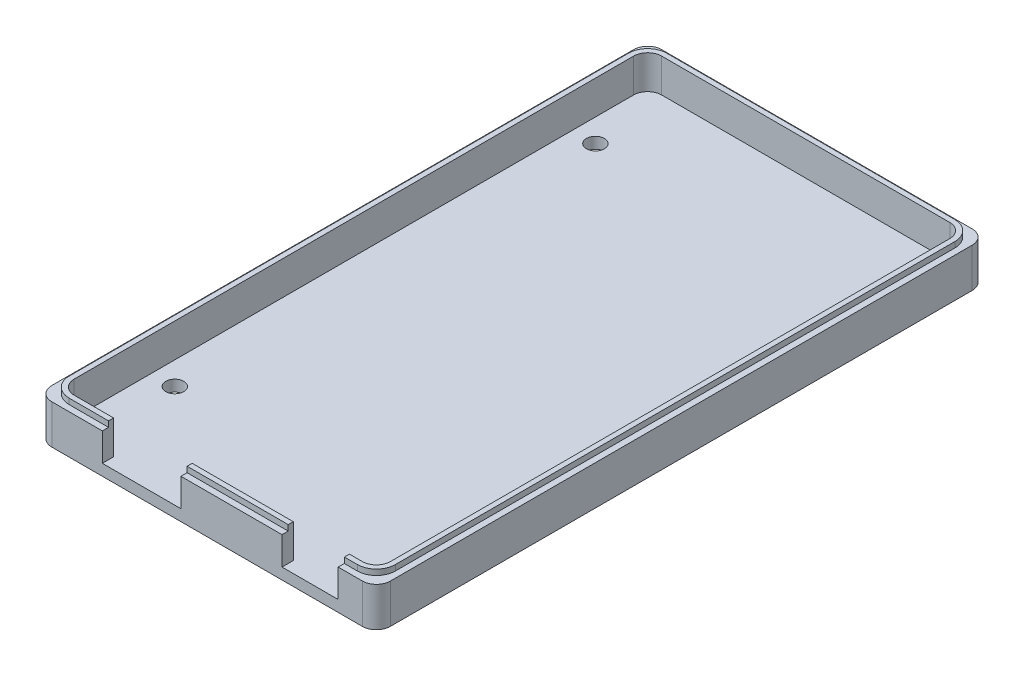
SolidWorks part; units mm, degrees
ref_plane "Front Plane" through (0, 0, 0) normal (0, 0, 1) x (1, 0, 0)
ref_plane "Top Plane" through (0, 0, 0) normal (0, 1, 0) x (1, 0, 0)
ref_plane "Right Plane" through (0, 0, 0) normal (1, 0, 0) x (0, 0, -1)
sketch "Sketch1" plane through (0, 0, 0) normal (0, 1, 0) x (1, 0, 0)
  line L0 (-12.8, 0) -> (-32.3, 0)
  line L1 (0, 0) -> (-3.8, 0)
  line L2 (0, 0) -> (0, 101.6)
  line L3 (0, 101.6) -> (-53.3, 101.6)
  line L4 (-53.3, 0) -> (-53.3, 101.6)
  line L5 (0, 0) -> (-53.3, 101.6) construction
  line L6 (0, 101.6) -> (-53.3, 0) construction
  line L7 (-44.3, -7) -> (-32.3, -7)
  line L8 (-44.3, -7) -> (-44.3, 0)
  line L10 (-32.3, -7) -> (-32.3, 0)
  line L11 (-44.3, -7) -> (-32.3, 0) construction
  line L12 (-44.3, 0) -> (-32.3, -7) construction
  line L13 (-3.8, -1.5) -> (-12.8, -1.5)
  line L14 (-3.8, -1.5) -> (-3.8, 0)
  line L16 (-12.8, -1.5) -> (-12.8, 0)
  line L17 (-3.8, -1.5) -> (-12.8, 0) construction
  line L18 (-3.8, 0) -> (-12.8, -1.5) construction
  line L19 (-44.3, 0) -> (-53.3, 0)
  circle A0 centre (-50.7, 14.8) radius 1.6
  circle A1 centre (-50.7, 89.7) radius 1.6
  circle A2 centre (-2.5, 13.5) radius 1.6
  circle A3 centre (-2.5, 96.52) radius 1.6
  circle A4 centre (-35.5, 65.6) radius 1.6
  circle A5 centre (-7.6, 65.6) radius 1.6
  point P4 (-26.65, 50.8)
  point P22 (-8.3, -0.75)
  point P23 (0, 0)
  point P24 (0, 0)
  point P30 (-38.3, -3.5)
  dimension "D11" = 3.2
  dimension "D1" = 53.3
  dimension "D2" = 101.6
  dimension "D3" = 2.5
  dimension "D4" = 5.1
  dimension "D5" = 27.9
  dimension "D6" = 15.2
  dimension "D7" = 13.5
  dimension "D8" = 1.3
  dimension "D9" = 50.8
  dimension "D10" = 24.1
  dimension "D12" = 9
  dimension "D13" = 12
  dimension "D14" = 3.8
  dimension "D15" = 9
  dimension "D16" = 7
  dimension "D17" = 1.5
  dimension "D18" = 96.52
sketch "Sketch2" plane through (0, 0, 0) normal (0, 1, 0) x (1, 0, 0)
  line L0 (0, 101.6) -> (-53.3, 101.6) construction
  line L1 (-53.3, 0) -> (-53.3, 101.6) construction
  line L2 (-44.3, 0) -> (-53.3, 0) construction
  line L3 (-44.3, -7) -> (-44.3, 0) construction
  line L4 (-12.8, -1.5) -> (-12.8, 0) construction
  line L5 (0, 0) -> (-3.8, 0) construction
  line L6 (-3.8, -1.5) -> (-3.8, 0) construction
  line L7 (-3.8, -1.5) -> (-12.8, -1.5) construction
  line L8 (0, 0) -> (0, 101.6) construction
  line L9 (-44.3, -7) -> (-32.3, -7) construction
  line L10 (-32.3, -7) -> (-32.3, 0) construction
  line L11 (-12.8, 0) -> (-32.3, 0) construction
  line L12 (0, 101.6) -> (-53.3, 101.6)
  line L13 (-53.3, 0) -> (-53.3, 101.6)
  line L14 (-44.3, 0) -> (-53.3, 0)
  line L15 (-44.3, -7) -> (-44.3, 0)
  line L16 (-12.8, -1.5) -> (-12.8, 0)
  line L17 (0, 0) -> (-3.8, 0)
  line L18 (-3.8, -1.5) -> (-3.8, 0)
  line L19 (-3.8, -1.5) -> (-12.8, -1.5)
  line L20 (0, 0) -> (0, 101.6)
  line L21 (-44.3, -7) -> (-32.3, -7)
  line L22 (-32.3, -7) -> (-32.3, 0)
  line L23 (-12.8, 0) -> (-32.3, 0)
  line L24 (-53.3, 67.5) -> (0, 67.5)
  line L25 (-4, 15) -> (-24, 15)
  line L26 (-4, 15) -> (-4, 30)
  line L27 (-4, 30) -> (-24, 30)
  line L28 (-24, 15) -> (-24, 30)
  line L29 (-4, 15) -> (-24, 30) construction
  line L30 (-4, 30) -> (-24, 15) construction
  line L31 (-29.3, 15) -> (-49.3, 15)
  line L32 (-29.3, 15) -> (-29.3, 30)
  line L33 (-29.3, 30) -> (-49.3, 30)
  line L34 (-49.3, 15) -> (-49.3, 30)
  line L35 (-29.3, 15) -> (-49.3, 30) construction
  line L36 (-29.3, 30) -> (-49.3, 15) construction
  line L37 (-4, 35) -> (-24, 35)
  line L38 (-4, 35) -> (-4, 50)
  line L39 (-4, 50) -> (-24, 50)
  line L40 (-24, 35) -> (-24, 50)
  line L41 (-4, 35) -> (-24, 50) construction
  line L42 (-4, 50) -> (-24, 35) construction
  line L43 (-29.3, 35) -> (-49.3, 35)
  line L44 (-29.3, 35) -> (-29.3, 50)
  line L45 (-29.3, 50) -> (-49.3, 50)
  line L46 (-49.3, 35) -> (-49.3, 50)
  line L47 (-29.3, 35) -> (-49.3, 50) construction
  line L48 (-29.3, 50) -> (-49.3, 35) construction
  line L50 (-46.3, 8) -> (-52.3, 8)
  line L51 (-46.3, 8) -> (-46.3, 2)
  line L52 (-46.3, 2) -> (-52.3, 2)
  line L53 (-52.3, 8) -> (-52.3, 2)
  line L54 (-46.3, 8) -> (-52.3, 2) construction
  line L55 (-46.3, 2) -> (-52.3, 8) construction
  line L56 (-16.5, 0) -> (-9, 0)
  line L57 (-16.5, 0) -> (-16.5, 10)
  line L58 (-16.5, 10) -> (-9, 10)
  line L59 (-9, 0) -> (-9, 10)
  line L60 (-16.5, 0) -> (-9, 10) construction
  line L61 (-16.5, 10) -> (-9, 0) construction
  line L62 (-37, 66.5) -> (-4, 66.5)
  line L63 (-37, 66.5) -> (-37, 61.5)
  line L64 (-37, 61.5) -> (-4, 61.5)
  line L65 (-4, 66.5) -> (-4, 61.5)
  line L66 (-37, 66.5) -> (-4, 61.5) construction
  line L67 (-37, 61.5) -> (-4, 66.5) construction
  circle A0 centre (-2.5, 13.5) radius 1.6 construction
  circle A1 centre (-50.7, 14.8) radius 1.6 construction
  circle A2 centre (-2.5, 96.52) radius 1.6 construction
  circle A3 centre (-50.7, 89.7) radius 1.6 construction
  circle A4 centre (-2.5, 13.5) radius 1.6
  circle A5 centre (-50.7, 14.8) radius 1.6
  circle A6 centre (-2.5, 96.52) radius 1.6
  circle A7 centre (-50.7, 89.7) radius 1.6
  point P26 (-14, 22.5)
  point P33 (-39.3, 22.5)
  point P38 (-14, 42.5)
  point P43 (-39.3, 42.5)
  point P50 (-49.3, 5)
  point P55 (-12.75, 5)
  point P60 (-20.5, 64)
  dimension "D1" = 15
  dimension "D2" = 20
  dimension "D3" = 20
  dimension "D4" = 4
  dimension "D5" = 4
  dimension "D6" = 15
  dimension "D7" = 5
  dimension "D8" = 5
  dimension "D9" = 15
  dimension "D10" = 17.5
  dimension "D11" = 2
  dimension "D12" = 1
  dimension "D13" = 6
  dimension "D14" = 6
  dimension "D15" = 9
  dimension "D16" = 7.5
  dimension "D17" = 10
  dimension "D18" = 5
  dimension "D19" = 4
  dimension "D20" = 1
  dimension "D21" = 33
sketch "Sketch4" plane through (0, 0, 0) normal (0, 1, 0) x (1, 0, 0)
  line L0 (-12.8, 0) -> (-32.3, 0) construction
  line L1 (-12.8, 0) -> (-32.3, 0) construction
  line L2 (-44.3, -7) -> (-32.3, -7) construction
  line L3 (-44.3, -7) -> (-32.3, -7) construction
  line L4 (0, 101.6) -> (-53.3, 101.6) construction
  line L5 (-53.3, 0) -> (-53.3, 101.6) construction
  line L6 (0, 0) -> (0, 101.6) construction
  line L7 (0, 0) -> (-3.8, 0) construction
  line L8 (-3.8, -1.5) -> (-3.8, 0) construction
  line L9 (-12.8, -1.5) -> (-12.8, 0) construction
  line L10 (-3.8, -1.5) -> (-12.8, -1.5) construction
  line L11 (-44.3, -7) -> (-44.3, 0) construction
  line L12 (-44.3, 0) -> (-53.3, 0) construction
  line L13 (-32.3, -7) -> (-32.3, 0) construction
  line L14 (0, 101.6) -> (-53.3, 101.6) construction
  line L15 (-53.3, 0) -> (-53.3, 101.6) construction
  line L16 (0, 0) -> (0, 101.6) construction
  line L17 (0, 0) -> (-3.8, 0) construction
  line L18 (-3.8, -1.5) -> (-3.8, 0) construction
  line L19 (-12.8, -1.5) -> (-12.8, 0) construction
  line L20 (-3.8, -1.5) -> (-12.8, -1.5) construction
  line L21 (-44.3, -7) -> (-44.3, 0) construction
  line L22 (-44.3, 0) -> (-53.3, 0) construction
  line L23 (-32.3, -7) -> (-32.3, 0) construction
  line L24 (-14.3, -1.5) -> (-30.8, -1.5)
  line L28 (-45.8, -1.5) -> (-54.8, -1.5)
  line L29 (-54.8, -1.5) -> (-54.8, 103.1)
  line L30 (1.5, 103.1) -> (-54.8, 103.1)
  line L31 (1.5, -1.5) -> (1.5, 103.1)
  line L32 (1.5, -1.5) -> (-2.3, -1.5)
  line L36 (-30.8, -1.5) -> (-45.8, -1.5)
  line L37 (-30.8, -8.5) -> (-30.8, -1.5) construction
  line L38 (-45.8, -8.5) -> (-30.8, -8.5) construction
  line L39 (-45.8, -8.5) -> (-45.8, -1.5) construction
  line L40 (-14.3, -1.5) -> (-2.3, -1.5)
  line L41 (-56.8, -3.5) -> (-56.8, 105.1)
  line L42 (-14.3, -3) -> (-14.3, -1.5) construction
  line L43 (-2.3, -3) -> (-14.3, -3) construction
  line L44 (-2.3, -3) -> (-2.3, -1.5) construction
  line L45 (3.5, 105.1) -> (-56.8, 105.1)
  line L46 (3.5, -3.5) -> (3.5, 105.1)
  line L47 (3.5, -3.5) -> (-2.3, -3.5)
  line L48 (-14.3, -3.5) -> (-2.3, -3.5)
  line L49 (-14.3, -3.5) -> (-30.8, -3.5)
  line L50 (-30.8, -3.5) -> (-45.8, -3.5)
  line L51 (-45.8, -3.5) -> (-56.8, -3.5)
  dimension "D1" = 1.5
  dimension "D2" = 2
extrude "Boss-Extrude1" add sketch "Sketch4" along normal blind 2 contours L51 L41 L45 L46 L47 L48 L49 L50
sketch "Sketch5" plane through (0, 2, 0) normal (0, 1, 0) x (1, 0, 0)
  line L0 (-54.8, -1.5) -> (-44.3, -1.5)
  line L1 (1.5, -1.5) -> (1.5, 103.1)
  line L2 (1.5, 103.1) -> (-54.8, 103.1)
  line L3 (-54.8, 103.1) -> (-54.8, -1.5)
  line L4 (-56.8, -3.5) -> (3.5, -3.5)
  line L5 (3.5, -3.5) -> (3.5, 105.1)
  line L6 (3.5, 105.1) -> (-56.8, 105.1)
  line L7 (-56.8, 105.1) -> (-56.8, -3.5)
  line L8 (-56.8, -3.5) -> (3.5, -3.5)
  line L9 (3.5, -3.5) -> (3.5, 105.1)
  line L10 (3.5, 105.1) -> (-56.8, 105.1)
  line L11 (-56.8, 105.1) -> (-56.8, -3.5)
  line L12 (-3.8, -1.5) -> (-3.8, 0) construction
  line L13 (-12.8, -1.5) -> (-12.8, 0) construction
  line L14 (-32.3, -7) -> (-32.3, 0) construction
  line L15 (-44.3, -7) -> (-44.3, 0) construction
  line L16 (-3.8, -1.5) -> (-3.8, 0) construction
  line L17 (-12.8, -1.5) -> (-12.8, 0) construction
  line L18 (-32.3, -7) -> (-32.3, 0) construction
  line L19 (-44.3, -7) -> (-44.3, 0) construction
  line L20 (-45.3, -3.5) -> (-45.3, -1.5)
  line L21 (-31.3, -3.5) -> (-31.3, -1.5)
  line L22 (-13.3, -1.5) -> (-13.3, 0) construction
  line L23 (-3.3, -1.5) -> (-3.3, 0) construction
  line L24 (-31.3, -7) -> (-31.3, 0) construction
  line L25 (-45.3, -7) -> (-45.3, 0) construction
  line L26 (-3.3, -1.5) -> (1.5, -1.5)
  line L27 (-54.8, -1.5) -> (1.5, -1.5) construction
  line L28 (-3.3, -1.5) -> (-3.3, -3.5)
  line L29 (1.5, -1.5) -> (1.5, 103.1) construction
  line L30 (-13.3, -1.5) -> (-32.3, -1.5)
  line L31 (-32.3, -1.5) -> (-32.3, -3.5)
  line L32 (3.5, -3.5) -> (-13.3, -3.5)
  line L33 (-13.3, -3.5) -> (-13.3, -1.5)
  line L34 (-3.8, -1.5) -> (-12.8, -1.5) construction
  dimension "D1" = 0
  dimension "D2" = 2
  dimension "D3" = 1
  dimension "D4" = 1
  dimension "D5" = 0.5
  dimension "D6" = 0.5
extrude "Boss-Extrude2" add sketch "Sketch5" along normal blind 5
sketch "Sketch6" plane through (0, 2, 0) normal (0, 1, 0) x (1, 0, 0)
  circle A0 centre (-2.5, 96.52) radius 1.6 construction
  circle A1 centre (-50.7, 89.7) radius 1.6 construction
  circle A2 centre (-2.5, 13.5) radius 1.6 construction
  circle A3 centre (-50.7, 14.8) radius 1.6 construction
  circle A4 centre (-2.5, 96.52) radius 1.6
  circle A5 centre (-50.7, 89.7) radius 1.6
  circle A6 centre (-2.5, 13.5) radius 1.6
  circle A7 centre (-50.7, 14.8) radius 1.6
extrude "Cut-Extrude1" cut sketch "Sketch6" against normal up to next
fillet "Fillet1" radius 2.5 8 edges at (-56.8, 3.5, 3.5) (3.5, 3.5, 3.5) (3.5, 3.5, -105.1) (-56.8, 3.5, -105.1) (1.5, 4.5, -103.1) (1.5, 4.5, 1.5) (-54.8, 4.5, -103.1) (-54.8, 4.5, 1.5)
sketch "Sketch7" plane through (0, 7, 0) normal (0, 1, 0) x (1, 0, 0)
  line L49 (-13.3, -1.5) -> (-31.3, -1.5) construction
  line L50 (-3.3, -1.5) -> (-1, -1.5) construction
  line L51 (1.5, 1) -> (1.5, 100.6) construction
  line L52 (-1, 103.1) -> (-52.3, 103.1) construction
  line L53 (-54.8, 100.6) -> (-54.8, 1) construction
  line L54 (-3.3, -2.4) -> (-1, -2.4)
  line L55 (2.4, 1) -> (2.4, 100.6)
  line L56 (-1, 104) -> (-52.3, 104)
  line L57 (-55.7, 100.6) -> (-55.7, 1)
  line L58 (-52.3, -2.4) -> (-45.3, -2.4)
  line L59 (-3.3, -2.4) -> (-1, -2.4)
  line L60 (2.4, 1) -> (2.4, 100.6)
  line L61 (-1, 104) -> (-52.3, 104)
  line L62 (-55.7, 100.6) -> (-55.7, 1)
  line L63 (-52.3, -2.4) -> (-45.3, -2.4)
  line L64 (-52.3, -1.5) -> (-45.3, -1.5) construction
  line L65 (-13.3, -1.5) -> (-31.3, -1.5)
  line L66 (-3.3, -1.5) -> (-1, -1.5)
  line L67 (1.5, 1) -> (1.5, 100.6)
  line L68 (-1, 103.1) -> (-52.3, 103.1)
  line L69 (-54.8, 100.6) -> (-54.8, 1)
  line L70 (-52.3, -1.5) -> (-45.3, -1.5)
  line L71 (-13.3, -2.4) -> (-31.3, -2.4)
  line L72 (-45.3, -2.4) -> (-45.3, -1.5)
  line L73 (-31.3, -2.4) -> (-31.3, -1.5)
  line L74 (-13.3, -2.4) -> (-13.3, -1.5)
  line L76 (-3.3, -1.5) -> (-3.3, -2.4)
  arc A35 (-1, -1.5) -> (1.5, 1) centre (-1, 1) ccw construction
  arc A36 (1.5, 100.6) -> (-1, 103.1) centre (-1, 100.6) ccw construction
  arc A37 (-52.3, 103.1) -> (-54.8, 100.6) centre (-52.3, 100.6) ccw construction
  arc A38 (-54.8, 1) -> (-52.3, -1.5) centre (-52.3, 1) ccw construction
  arc A39 (-1, -2.4) -> (2.4, 1) centre (-1, 1) ccw
  arc A40 (2.4, 100.6) -> (-1, 104) centre (-1, 100.6) ccw
  arc A41 (-52.3, 104) -> (-55.7, 100.6) centre (-52.3, 100.6) ccw
  arc A42 (-55.7, 1) -> (-52.3, -2.4) centre (-52.3, 1) ccw
  arc A43 (-1, -2.4) -> (2.4, 1) centre (-1, 1) ccw
  arc A44 (2.4, 100.6) -> (-1, 104) centre (-1, 100.6) ccw
  arc A45 (-52.3, 104) -> (-55.7, 100.6) centre (-52.3, 100.6) ccw
  arc A46 (-55.7, 1) -> (-52.3, -2.4) centre (-52.3, 1) ccw
  arc A47 (-1, -1.5) -> (1.5, 1) centre (-1, 1) ccw
  arc A48 (1.5, 100.6) -> (-1, 103.1) centre (-1, 100.6) ccw
  arc A49 (-52.3, 103.1) -> (-54.8, 100.6) centre (-52.3, 100.6) ccw
  arc A50 (-54.8, 1) -> (-52.3, -1.5) centre (-52.3, 1) ccw
  dimension "D1" = 0.9
  dimension "D2" = 0.9
extrude "Boss-Extrude3" add sketch "Sketch7" along normal blind 1
